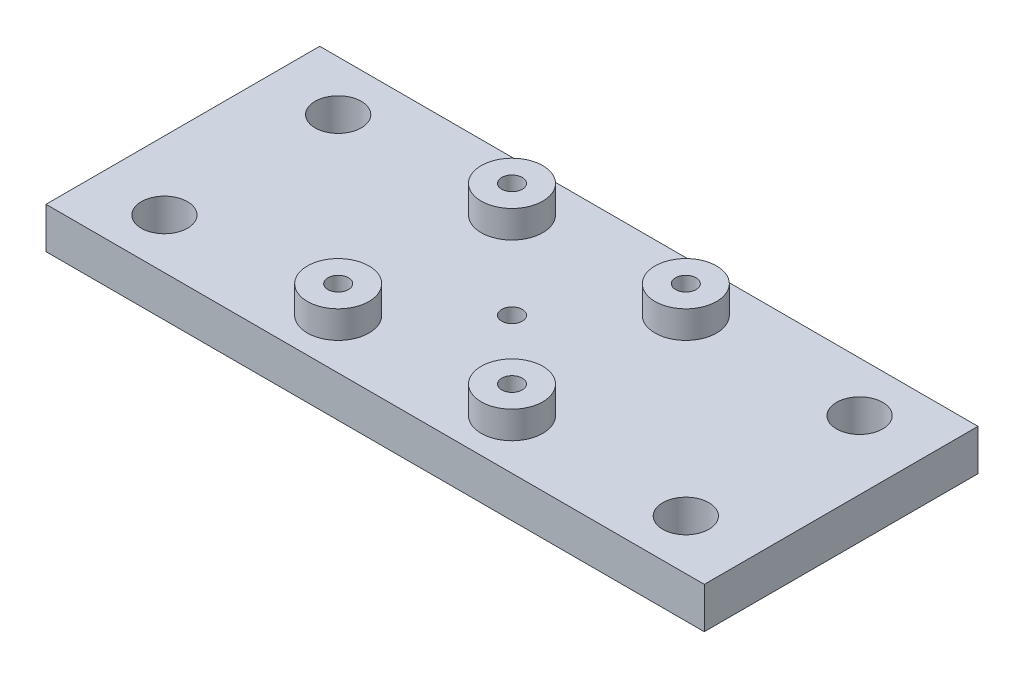
SolidWorks part; units mm, degrees
ref_plane "Front Plane" through (0, 0, 0) normal (0, 0, 1) x (1, 0, 0)
ref_plane "Top Plane" through (0, 0, 0) normal (0, 1, 0) x (1, 0, 0)
ref_plane "Right Plane" through (0, 0, 0) normal (1, 0, 0) x (0, 0, -1)
sketch "Sketch2" plane through (0, 0, 0) normal (0, 1, 0) x (1, 0, 0)
  line L0 (50.6319, 72.4554) -> (90.6319, 32.4554) construction
  line L5 (50.6319, 32.4554) -> (90.6319, 72.4554) construction
  line L6 (32.5319, 72.4554) -> (32.5319, 32.4554) construction
  line L7 (90.6319, 32.4554) -> (50.6319, 32.4554)
  line L8 (90.6319, 32.4554) -> (90.6319, 72.4554)
  line L9 (90.6319, 72.4554) -> (50.6319, 72.4554)
  line L10 (50.6319, 32.4554) -> (50.6319, 72.4554)
  line L11 (90.6319, 32.4554) -> (50.6319, 72.4554) construction
  line L12 (90.6319, 72.4554) -> (50.6319, 32.4554) construction
  line L13 (118.7319, 32.4554) -> (22.5319, 32.4554)
  line L14 (118.7319, 32.4554) -> (118.7319, 72.4554)
  line L15 (118.7319, 72.4554) -> (22.5319, 72.4554)
  line L16 (22.5319, 32.4554) -> (22.5319, 72.4554)
  line L17 (118.7319, 32.4554) -> (22.5319, 72.4554) construction
  line L18 (118.7319, 72.4554) -> (22.5319, 32.4554) construction
  line L19 (108.7319, 72.4554) -> (108.7319, 32.4554) construction
  circle A0 centre (57.9319, 65.1554) radius 1.5
  circle A1 centre (83.3319, 65.1554) radius 1.5
  circle A2 centre (83.3319, 39.7554) radius 1.5
  circle A3 centre (57.9319, 39.7554) radius 1.5
  circle A8 centre (32.5319, 65.1554) radius 3.3734
  circle A9 centre (32.5319, 39.7554) radius 3.3734
  circle A10 centre (108.7319, 65.1554) radius 3.3734
  circle A11 centre (108.7319, 39.7554) radius 3.3734
  circle A12 centre (70.6319, 52.4554) radius 1.5
  point P1 (108.7319, 52.4554)
  point P5 (70.6319, 52.4554)
  point P19 (70.6319, 52.4554)
  point P31 (32.5319, 52.4554)
  dimension "D3" = 6.7469
  dimension "D4" = 0
  dimension "D5" = 12.7
  dimension "D6" = 12.7
  dimension "D7" = 40
  dimension "D8" = 76.2
  dimension "D9" = 10
  dimension "D10" = 3
  dimension "D16" = 3
  dimension "D1" = 40
  dimension "D2" = 10
  dimension "D11" = 0
  dimension "D12" = 0
  dimension "D13" = 0
  dimension "D14" = 0
  dimension "D15" = 12.7
extrude "Boss-Extrude1" add sketch "Sketch2" along normal blind 6 contours L16 L13 L10 L15 A9 A8 | A3 L13 A2 L8 L15 A1 A0 L10 | A1 L15 L8 L9 L10 A0 | A3 L13 L10 L7 L8 A2 | L14 L15 L8 L13 A11 A10
sketch "Sketch3" plane through (0, 6, 0) normal (0, 1, 0) x (1, 0, 0)
  circle A0 centre (57.9319, 65.1554) radius 1.5
  circle A1 centre (57.9319, 65.1554) radius 4.5
  circle A2 centre (57.9319, 65.1554) radius 1.5 construction
  dimension "D1" = 9
extrude "Boss-Extrude2" add sketch "Sketch3" along normal blind 4
ref_plane "Plane1" through (70.6319, 0, 0) normal (-1, 0, 0) x (0, 0, 1)
mirror "Mirror1" about plane through (70.6319, 0, 0) normal (-1, 0, 0) of "Boss-Extrude2"
ref_plane "Plane2" through (0, 0, -52.4554) normal (0, 0, -1) x (-1, 0, 0)
mirror "Mirror2" about plane through (0, 0, -52.4554) normal (0, 0, -1) of "Mirror1", "Boss-Extrude2"
sketch "Sketch5" plane through (0, 0, 0) normal (0, -1, 0) x (1, 0, 0)
  circle A0 centre (70.6319, -52.4554) radius 2.75
  dimension "D1" = 5.5
extrude "Cut-Extrude1" cut sketch "Sketch5" against normal blind 3.3
